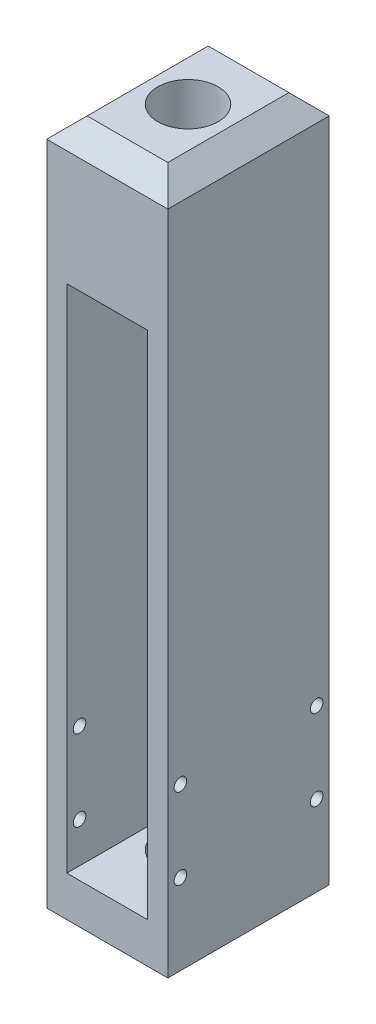
SolidWorks part; units mm, degrees
material "6061-T6 (SS)"
ref_plane "Front Plane" through (0, 0, 0) normal (0, 0, 1) x (1, 0, 0)
ref_plane "Top Plane" through (0, 0, 0) normal (0, 1, 0) x (1, 0, 0)
ref_plane "Right Plane" through (0, 0, 0) normal (1, 0, 0) x (0, 0, -1)
sketch "Sketch1" plane through (0, 0, 0) normal (0, 0, 1) x (1, 0, 0)
  line L1 (0, 0) -> (38.1, 0)
  line L2 (0, 0) -> (0, 215.9)
  line L3 (0, 215.9) -> (38.1, 215.9)
  line L4 (38.1, 0) -> (38.1, 215.9)
  line L5 (6.35, 12.7) -> (31.75, 12.7)
  line L6 (6.35, 12.7) -> (6.35, 173.355)
  line L7 (6.35, 173.355) -> (31.75, 173.355)
  line L8 (31.75, 12.7) -> (31.75, 173.355)
  dimension "D1" = 38.1
  dimension "D2" = 25.4
  dimension "D3" = 6.35
  dimension "D4" = 215.9
  dimension "D5" = 42.545
  dimension "D6" = 12.7
extrude "Boss-Extrude1" add sketch "Sketch1" along normal blind 50.8
hole_wizard "3/4 (0.75) Diameter Hole1" positions "Sketch2" profile "Sketch3" hole size "3/4" standard "ANSI Inch" end condition up to next
sketch "Sketch2" plane through (0, 0, 0) normal (0, -1, 0) x (-1, 0, 0)
  line L0 (0, 0) -> (-38.1, 0) construction
  line L1 (0, -50.8) -> (0, 0) construction
  point P0 (-19.05, -25.4)
  point P7 (-19.05, 0)
  point P11 (0, -25.4)
sketch "Sketch3" plane through (19.05, 0, 25.4) normal (1, 0, 0) x (0, 0, -1)
  line L0 (0, 0) -> (0, 12.7)
  line L1 (0, 12.7) -> (9.525, 12.7)
  line L2 (9.525, 12.7) -> (9.525, 0)
  line L5 (9.525, 0) -> (0, 0)
  line L11 (0, -6.35) -> (0, 107.95) construction
  dimension "Thru Hole Dia." = 19.05
  dimension "Thru Hole Depth" = 12.7
hole_wizard "3/4 (0.75) Diameter Hole2" positions "Sketch4" profile "Sketch5" hole size "3/4" standard "ANSI Inch" end condition up to next
sketch "Sketch4" plane through (0, 215.9, 0) normal (0, 1, 0) x (1, 0, 0)
  line L0 (38.1, -50.8) -> (0, -50.8) construction
  line L1 (0, -50.8) -> (0, 0) construction
  point P0 (19.05, -25.4)
  point P6 (19.05, -50.8)
  point P9 (0, -25.4)
sketch "Sketch5" plane through (19.05, 215.9, 25.4) normal (1, 0, 0) x (0, 0, 1)
  line L0 (0, 0) -> (0, 42.545)
  line L1 (0, 42.545) -> (9.525, 42.545)
  line L2 (9.525, 42.545) -> (9.525, 0)
  line L5 (9.525, 0) -> (0, 0)
  line L11 (0, -6.35) -> (0, 107.95) construction
  dimension "Thru Hole Dia." = 19.05
  dimension "Thru Hole Depth" = 42.545
hole_wizard "5/32 (0.15625) Diameter Hole1" positions "Sketch6" profile "Sketch7" hole size "5/32" standard "ANSI Inch"
sketch "Sketch6" plane through (38.1, 0, 0) normal (1, 0, 0) x (0, 0, -1)
  line L0 (-50.8, 0) -> (0, 0) construction
  line L2 (-50.8, 0) -> (-50.8, 215.9) construction
  point P0 (-46.8312, 25.4)
  point P2 (-3.9688, 25.4)
  point P4 (-3.9688, 50.8)
  point P6 (-46.8312, 50.8)
  dimension "D1" = 25.4
  dimension "D2" = 42.8625
  dimension "D3" = 25.4
  dimension "D4" = 3.9688
sketch "Sketch7" plane through (38.1, 25.4, 46.8312) normal (0, 1, 0) x (0, 0, -1)
  line L0 (0, 0) -> (0, 38.1)
  line L1 (0, 38.1) -> (1.9844, 38.1)
  line L2 (1.9844, 38.1) -> (1.9844, 0)
  line L5 (1.9844, 0) -> (0, 0)
  line L11 (0, -6.35) -> (0, 107.95) construction
  dimension "Thru Hole Dia." = 3.9688
  dimension "Thru Hole Depth" = 38.1
ref_plane "Plane1" through (19.05, 0, 0) normal (1, 0, 0) x (0, 0, -1)
mirror "Mirror1" about plane through (19.05, 0, 0) normal (1, 0, 0) of "5/32 (0.15625) Diameter Hole1"
chamfer "Chamfer1" distance 6.35 angle 45 4 edges at (19.05, 215.9, 0) (0, 215.9, 25.4) (38.1, 215.9, 25.4) (19.05, 215.9, 50.8)
